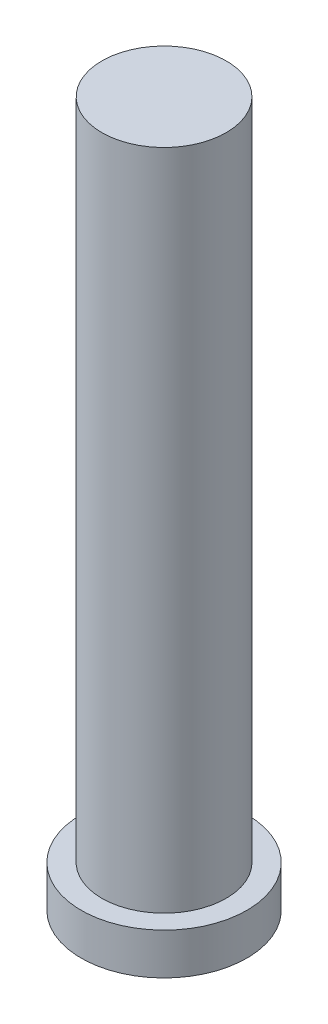
SolidWorks part; units mm, degrees
ref_plane "前视基准面" through (0, 0, 0) normal (0, 0, 1) x (1, 0, 0)
ref_plane "上视基准面" through (0, 0, 0) normal (0, 1, 0) x (1, 0, 0)
ref_plane "右视基准面" through (0, 0, 0) normal (1, 0, 0) x (0, 0, -1)
other "Configuration Table"
sketch "草图2" plane through (0, 0, 0) normal (0, 1, 0) x (1, 0, 0)
  circle A0 centre (0, 0) radius 0.75
  dimension "D1" = 1.5
extrude "凸台-拉伸1" add sketch "草图2" along normal blind 8
sketch "草图3" plane through (0, 0, 0) normal (0, -1, 0) x (1, 0, 0)
  circle A0 centre (0, 0) radius 1
  dimension "D1" = 2
extrude "凸台-拉伸2" add sketch "草图3" along normal blind 0.5
